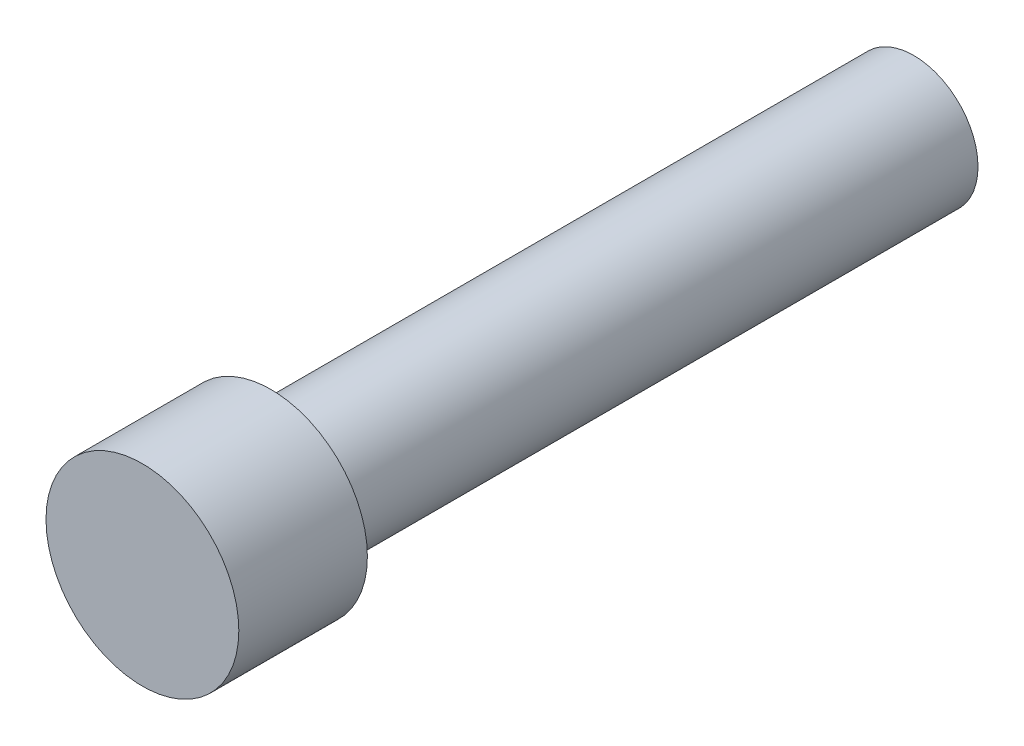
SolidWorks part; units mm, degrees
ref_plane "Front Plane" through (0, 0, 0) normal (0, 0, 1) x (1, 0, 0)
ref_plane "Top Plane" through (0, 0, 0) normal (0, 1, 0) x (1, 0, 0)
ref_plane "Right Plane" through (0, 0, 0) normal (1, 0, 0) x (0, 0, -1)
sketch "Sketch1" plane through (0, 0, 0) normal (0, 0, 1) x (1, 0, 0)
  circle A0 centre (0, 0) radius 3.175
  dimension "D1" = 6.35
extrude "Boss-Extrude1" add sketch "Sketch1" along normal blind 31.75
sketch "Sketch2" plane through (0, 0, 31.75) normal (0, 0, 1) x (1, 0, 0)
  circle A0 centre (0, 0) radius 4.7625
  dimension "D1" = 9.525
extrude "Boss-Extrude2" add sketch "Sketch2" along normal blind 6.35
